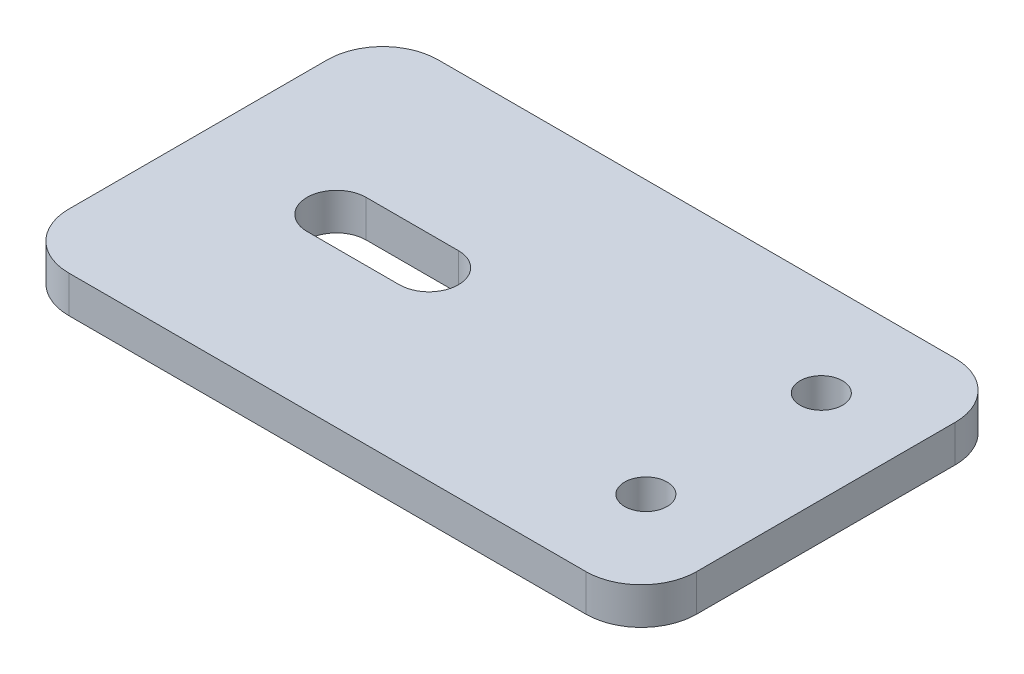
SolidWorks part; units mm, degrees
material "E-玻璃纤维"
ref_plane "前视基准面" through (0, 0, 0) normal (0, 0, 1) x (1, 0, 0)
ref_plane "上视基准面" through (0, 0, 0) normal (0, 1, 0) x (1, 0, 0)
ref_plane "右视基准面" through (0, 0, 0) normal (1, 0, 0) x (0, 0, -1)
sketch "草图1" plane through (0, 0, 0) normal (0, 1, 0) x (1, 0, 0)
  line L0 (0, 0) -> (46.2325, 0) construction
  line L1 (-10, 10) -> (10, 10)
  line L2 (-10, 10) -> (-10, -10)
  line L3 (-10, -10) -> (10, -10)
  line L5 (-10, 10) -> (10, -10) construction
  line L6 (-10, -10) -> (10, 10) construction
  line L7 (10, 10) -> (10, -10) construction
  line L8 (10, 10) -> (24, 10)
  line L10 (10, -10) -> (24, -10)
  line L11 (24, 10) -> (24, -10)
  circle A0 centre (0, 0) radius 1.6
  circle A5 centre (19, -4.75) radius 1.15
  circle A6 centre (19, 4.75) radius 1.15
  point P0 (0, 0)
  dimension "D1" = 3.2
  dimension "D4" = 9.5
  dimension "D5" = 2.3
  dimension "D2" = 20
  dimension "D3" = 20
  dimension "D6" = 9
  dimension "D7" = 5
extrude "凸台-拉伸1" add sketch "草图1" along normal blind 2
fillet "圆角2" radius 3 4 edges at (-10, 1, -10) (-10, 1, 10) (24, 1, -10) (24, 1, 10)
sketch "草图2" plane through (0, 2, 0) normal (0, 1, 0) x (1, 0, 0)
  line L0 (2.5, 0) -> (-2.5, 0) construction
  line L1 (2.5, -1.6) -> (-2.5, -1.6)
  line L2 (2.5, 1.6) -> (-2.5, 1.6)
  arc A0 (2.5, -1.6) -> (2.5, 1.6) centre (2.5, 0) ccw
  arc A1 (-2.5, 1.6) -> (-2.5, -1.6) centre (-2.5, 0) ccw
  point P2 (0, 0)
  dimension "D1" = 3.2
  dimension "D2" = 5
extrude "切除-拉伸1" cut sketch "草图2" against normal blind 10
